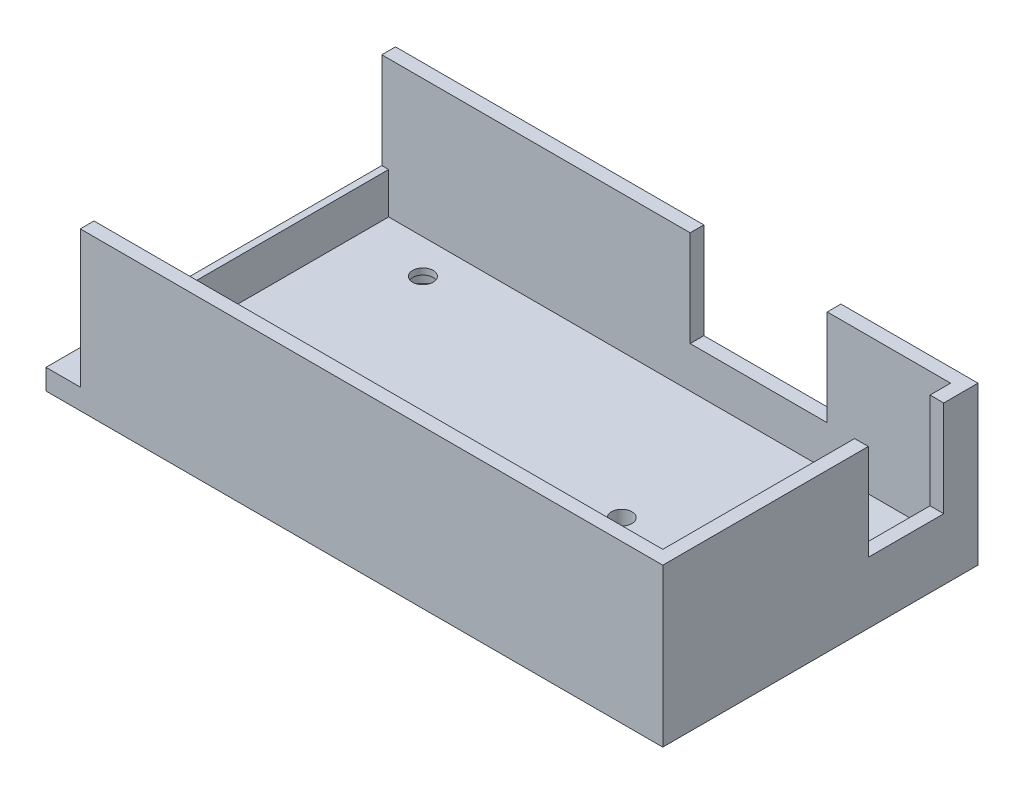
SolidWorks part; units mm, degrees
ref_plane "Front Plane" through (0, 0, 0) normal (0, 0, 1) x (1, 0, 0)
ref_plane "Top Plane" through (0, 0, 0) normal (0, 1, 0) x (1, 0, 0)
ref_plane "Right Plane" through (0, 0, 0) normal (1, 0, 0) x (0, 0, -1)
sketch "Sketch1" plane through (0, 0, 0) normal (0, 1, 0) x (1, 0, 0)
  line L1 (-60.2291, 12.7329) -> (29.7709, 12.7329)
  line L2 (-60.2291, 12.7329) -> (-60.2291, -33.2671)
  line L3 (-60.2291, -33.2671) -> (29.7709, -33.2671)
  line L4 (29.7709, 12.7329) -> (29.7709, -33.2671)
  dimension "D1" = 46
  dimension "D2" = 90
extrude "Boss-Extrude1" add sketch "Sketch1" along normal blind 3 contours L2 L1 L4 L3
sketch "Sketch5" plane through (0, 3, 0) normal (0, 1, 0) x (1, 0, 0)
  line L1 (-60.2291, -33.2671) -> (29.7709, -33.2671) construction
  line L2 (29.7709, 12.7329) -> (29.7709, -33.2671) construction
  circle A0 centre (-57.2291, -22.2671) radius 1.5
  circle A1 centre (-57.2291, 1.7329) radius 1.5
  circle A2 centre (0.7709, -10.2671) radius 1.5
  dimension "D1" = 3
  dimension "D2" = 3
  dimension "D3" = 3
  dimension "D4" = 58
  dimension "D5" = 11
  dimension "D6" = 58
  dimension "D7" = 24
  dimension "D8" = 23
  dimension "D9" = 29
extrude "Cut-Extrude3" cut sketch "Sketch5" against normal through all
sketch "Sketch6" plane through (0, 3, 0) normal (0, 1, 0) x (1, 0, 0)
  line L5 (-60.2291, -33.2671) -> (29.7709, -33.2671) construction
  line L10 (-60.2291, 12.7329) -> (29.7709, 12.7329) construction
  line L11 (29.7709, 12.7329) -> (29.7709, -33.2671) construction
  line L12 (27.7709, -31.2671) -> (29.7709, -31.2671)
  line L13 (27.7709, -31.2671) -> (27.7709, -3.2671)
  line L14 (27.7709, -3.2671) -> (29.7709, -3.2671)
  line L15 (29.7709, -31.2671) -> (29.7709, -3.2671)
  line L16 (-55.2291, -33.2671) -> (4.7709, -33.2671)
  line L17 (27.7709, 7.7329) -> (29.7709, 7.7329)
  line L18 (27.7709, 7.7329) -> (27.7709, 10.7329)
  line L19 (27.7709, 10.7329) -> (29.7709, 10.7329)
  line L20 (29.7709, 7.7329) -> (29.7709, 10.7329)
  line L25 (4.7709, -33.2671) -> (29.7709, -33.2671)
  line L26 (4.7709, -33.2671) -> (4.7709, -31.2671)
  line L27 (4.7709, -31.2671) -> (29.7709, -31.2671)
  line L28 (29.7709, -33.2671) -> (29.7709, -31.2671)
  line L33 (9.7709, 10.7329) -> (29.7709, 10.7329)
  line L34 (9.7709, 10.7329) -> (9.7709, 12.7329)
  line L35 (9.7709, 12.7329) -> (29.7709, 12.7329)
  line L36 (29.7709, 10.7329) -> (29.7709, 12.7329)
  line L37 (-55.2291, -33.2671) -> (-55.2291, -31.2671)
  line L38 (-55.2291, -31.2671) -> (4.7709, -31.2671)
  line L39 (4.7709, -33.2671) -> (4.7709, -31.2671)
  line L43 (-55.2291, 10.7329) -> (-10.2291, 10.7329)
  line L44 (-55.2291, 10.7329) -> (-55.2291, 12.7329)
  line L45 (-55.2291, 12.7329) -> (-10.2291, 12.7329)
  line L46 (-10.2291, 10.7329) -> (-10.2291, 12.7329)
  point P4 (29.7709, -32.2671)
  point P5 (4.7709, -32.2671)
  point P28 (-10.2291, 11.7329)
  point P41 (29.7709, 11.7329)
  line M33 (29.7709, -33.2671) -> (29.7709, 12.7329)
  line M34 (29.7709, 12.7329) -> (-60.2291, 12.7329)
  line M35 (-60.2291, 12.7329) -> (-60.2291, -33.2671)
  dimension "D4" = 2
  dimension "D5" = 85
  dimension "D6" = 0
  dimension "D7" = 0
  dimension "D8" = 85
  dimension "D9" = 28
  dimension "D10" = 2
  dimension "D11" = 0
  dimension "D12" = 0
  dimension "D13" = 3
  dimension "D14" = 2
  dimension "D15" = 0
  dimension "D16" = 0
  dimension "D17" = 0
  dimension "D18" = 2
  dimension "D19" = 20
  dimension "D25" = 20
  dimension "D26" = 0
  dimension "D27" = 0
  dimension "D28" = 2
  dimension "D29" = 25
  dimension "D30" = 2
  dimension "D31" = 0
  dimension "D32" = 0
extrude "Boss-Extrude3" add sketch "Sketch6" along normal blind 20 contours L16 L39 L38 M35 | L34 L33 L19 M33 M34
sketch "Sketch7" plane through (0, 3, 0) normal (0, 1, 0) x (1, 0, 0)
  line L1 (-60.2291, -33.2671) -> (-55.2291, -33.2671) construction
  circle A0 centre (15.7709, -26.2671) radius 1.5
  circle A1 centre (-44.2291, -26.2671) radius 1.5
  circle A2 centre (15.7709, 5.7329) radius 1.5
  circle A3 centre (-44.2291, 5.7329) radius 1.5
  circle A6 centre (0.7709, -10.2671) radius 1.5 construction
  dimension "D1" = 3
  dimension "D2" = 3
  dimension "D3" = 3
  dimension "D4" = 3
  dimension "D5" = 32
  dimension "D10" = 15
  dimension "D6" = 60
  dimension "D7" = 60
  dimension "D8" = 32
  dimension "D9" = 15
  dimension "D11" = 7
  dimension "D12" = 7
extrude "Cut-Extrude4" cut sketch "Sketch7" against normal through all
sketch "Sketch8" plane through (0, 0, 0) normal (0, -1, 0) x (-1, 0, 0)
  circle A0 centre (-15.7709, -26.2671) radius 3
  circle A1 centre (-15.7709, 5.7329) radius 3
  circle A2 centre (44.2291, -26.2671) radius 3
  circle A3 centre (44.2291, 5.7329) radius 3
  circle A4 centre (-15.7709, -26.2671) radius 1.5 construction
  circle A5 centre (-15.7709, 5.7329) radius 1.5 construction
  circle A7 centre (44.2291, -26.2671) radius 1.5 construction
  circle A8 centre (44.2291, 5.7329) radius 1.5 construction
  dimension "D1" = 6
  dimension "D2" = 6
  dimension "D3" = 6
  dimension "D4" = 6
  dimension "D5" = 0
  dimension "D6" = 0
extrude "Cut-Extrude5" cut sketch "Sketch8" against normal blind 2.1
sketch "Sketch9" plane through (0, 3, 0) normal (0, 1, 0) x (1, 0, 0)
  line L0 (27.7709, -3.2671) -> (29.7709, -3.2671) construction
  line L1 (29.7709, -3.2671) -> (27.7709, -3.2671)
  line L2 (29.7709, -3.2671) -> (29.7709, 7.7329)
  line L3 (29.7709, 7.7329) -> (27.7709, 7.7329)
  line L4 (27.7709, -3.2671) -> (27.7709, 7.7329)
  line L5 (9.7709, 10.7329) -> (-10.2291, 10.7329)
  line L6 (9.7709, 10.7329) -> (9.7709, 12.7329)
  line L7 (9.7709, 12.7329) -> (-10.2291, 12.7329)
  line L8 (-10.2291, 10.7329) -> (-10.2291, 12.7329)
  line L13 (29.7709, 7.7329) -> (29.7709, -3.2671) construction
  line L14 (27.7709, 7.7329) -> (29.7709, 7.7329) construction
  line L15 (-10.2291, 12.7329) -> (9.7709, 12.7329) construction
  line L16 (9.7709, 10.7329) -> (9.7709, 12.7329) construction
  line L17 (-10.2291, 10.7329) -> (-10.2291, 12.7329) construction
  line L18 (-55.2291, -31.2671) -> (27.7709, -31.2671) construction
  line L19 (-54.2291, -31.2671) -> (-55.2291, -31.2671)
  line L20 (-54.2291, -31.2671) -> (-54.2291, 10.7329)
  line L24 (-54.2291, 10.7329) -> (-55.2291, 10.7329)
  line L25 (-55.2291, -31.2671) -> (-55.2291, 10.7329)
  line L26 (-55.2291, 10.7329) -> (-10.2291, 10.7329) construction
  line L27 (-55.2291, 10.7329) -> (-55.2291, 12.7329) construction
  dimension "D1" = 2
  dimension "D2" = 2
  dimension "D3" = 1
  dimension "D4" = 0
  dimension "D5" = 0
  dimension "D6" = 0
  dimension "D7" = 0
  dimension "D8" = 0
  dimension "D9" = 0
  dimension "D10" = 0
  dimension "D11" = 0
  dimension "D12" = 0
extrude "Boss-Extrude4" add sketch "Sketch9" along normal blind 6
